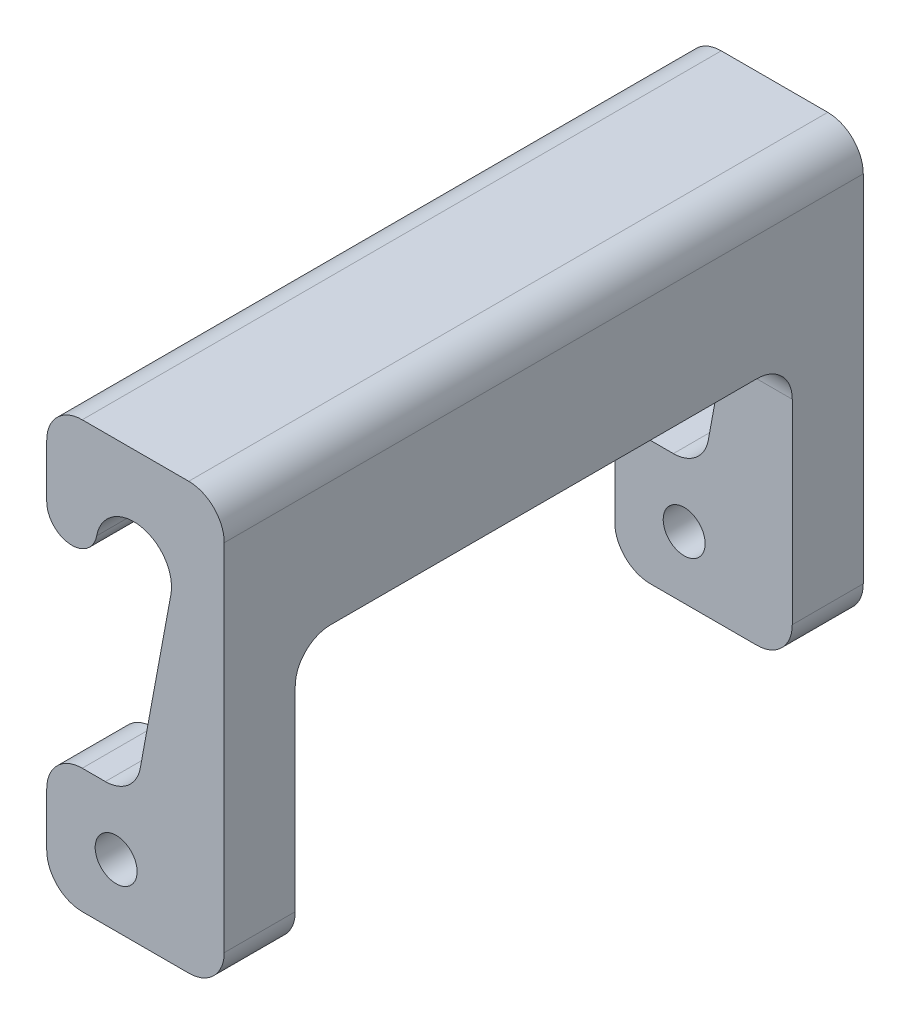
SolidWorks part; units mm, degrees
ref_plane "Front Plane" through (0, 0, 0) normal (0, 0, 1) x (1, 0, 0)
ref_plane "Top Plane" through (0, 0, 0) normal (0, 1, 0) x (1, 0, 0)
ref_plane "Right Plane" through (0, 0, 0) normal (1, 0, 0) x (0, 0, -1)
sketch "Sketch1" plane through (0, 0, 0) normal (0, 0, 1) x (1, 0, 0)
  line L0 (8.8822, 22.8213) -> (6.6916, 10.9684)
  line L1 (2.54, 0) -> (10.16, 0)
  line L2 (0, 2.54) -> (0, 6.35)
  line L3 (2.54, 30.48) -> (10.16, 30.48)
  line L4 (12.7, 2.54) -> (12.7, 27.94)
  line L5 (4.1939, 8.89) -> (2.54, 8.89)
  line L6 (0, 24.13) -> (0, 27.94)
  arc A0 (0, 24.13) -> (3.5716, 23.8027) centre (1.8008, 24.13) ccw
  arc A1 (3.5716, 23.8027) -> (8.8822, 22.8213) centre (6.2269, 23.312) cw
  arc A2 (6.6916, 10.9684) -> (4.1939, 8.89) centre (4.1939, 11.43) cw
  circle A3 centre (4.9655, 4.445) radius 1.5
  arc A4 (10.16, 0) -> (12.7, 2.54) centre (10.16, 2.54) ccw
  arc A5 (10.16, 30.48) -> (12.7, 27.94) centre (10.16, 27.94) cw
  arc A6 (0, 27.94) -> (2.54, 30.48) centre (2.54, 27.94) cw
  arc A7 (2.54, 0) -> (0, 2.54) centre (2.54, 2.54) cw
  arc A8 (2.54, 8.89) -> (0, 6.35) centre (2.54, 6.35) ccw
  point P20 (12.7, 0)
  point P25 (0, 30.48)
  point P28 (0, 0)
  dimension "D3" = 2.54
  dimension "D5" = 2.54
  dimension "D6" = 3
  dimension "D7" = 2.54
  dimension "D1" = 12.7
  dimension "D2" = 30.48
  dimension "D4" = 19.685
  dimension "D8" = 4.445
  dimension "D9" = 8.89
extrude "Boss-Extrude1" add sketch "Sketch1" along normal blind 45.72 contours A7 L1 A4 L4 A5 L3 A6 L2 A0 A1 L0 A2 L5 A3
sketch "Sketch2" plane through (12.7, 0, 0) normal (1, 0, 0) x (0, 0, -1)
  line L0 (-45.72, 0) -> (0, 0) construction
  line L1 (-40.64, 0) -> (-5.08, 0)
  line L2 (-40.64, 0) -> (-40.64, 16.51)
  line L3 (-38.1, 19.05) -> (-7.62, 19.05)
  line L4 (-5.08, 0) -> (-5.08, 16.51)
  line L5 (-45.72, 2.54) -> (-45.72, 27.94) construction
  line L6 (0, 2.54) -> (0, 27.94) construction
  arc A0 (-7.62, 19.05) -> (-5.08, 16.51) centre (-7.62, 16.51) cw
  arc A1 (-40.64, 16.51) -> (-38.1, 19.05) centre (-38.1, 16.51) cw
  dimension "D4" = 2.54
  dimension "D1" = 5.08
  dimension "D2" = 5.08
  dimension "D3" = 19.05
extrude "Cut-Extrude1" cut sketch "Sketch2" against normal blind 25.4
